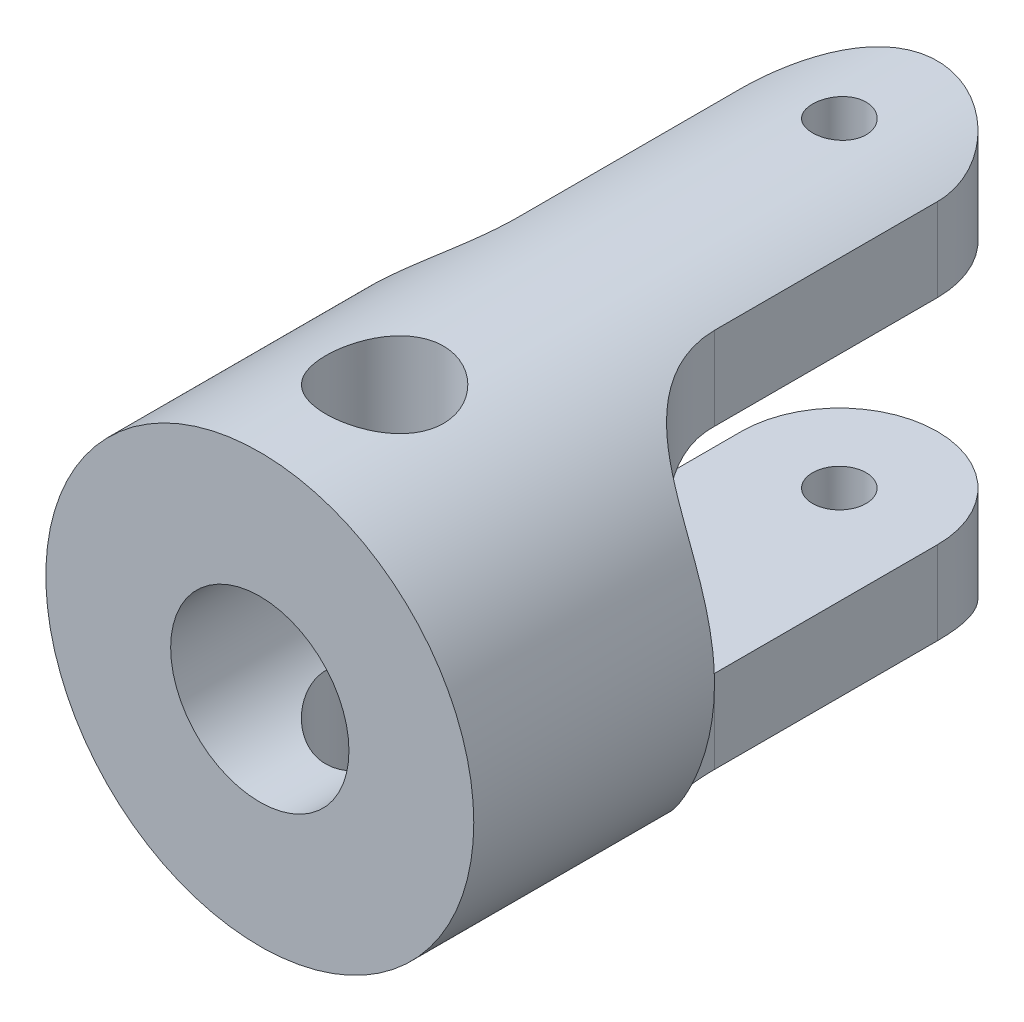
SolidWorks part; units mm, degrees
ref_plane "前视基准面" through (0, 0, 0) normal (0, 0, 1) x (1, 0, 0)
ref_plane "上视基准面" through (0, 0, 0) normal (0, 1, 0) x (1, 0, 0)
ref_plane "右视基准面" through (0, 0, 0) normal (1, 0, 0) x (0, 0, -1)
sketch "草图1" plane through (0, 0, 0) normal (0, 0, 1) x (1, 0, 0)
  circle A0 centre (0, 0) radius 6
  circle A1 centre (0, 0) radius 2.5
  dimension "D1" = 12
  dimension "D2" = 5
extrude "凸台-拉伸1" add sketch "草图1" along normal blind 19
sketch "草图2" plane through (0, 0, 0) normal (0, 1, 0) x (1, 0, 0)
  line L0 (0, 3.1848) -> (0, -21.7389) construction
  line L1 (-11.4446, -9) -> (14.3905, -9) construction
  line L2 (-2.75, -2.75) -> (-2.75, -9)
  line L4 (-6, 0) -> (-6, -19) construction
  line L5 (-6, -19) -> (6, -19) construction
  line L6 (-6, -2.0062) -> (-6, -15.979) construction
  line L7 (-6, -12.25) -> (-6, -19)
  line L8 (-6, -19) -> (6, -19)
  line L9 (6, -12.25) -> (6, -19)
  line L10 (2.75, -2.75) -> (2.75, -9)
  arc A0 (2.75, -2.75) -> (-2.75, -2.75) centre (0, -2.75) ccw
  arc A2 (-6, -12.25) -> (-2.75, -9) centre (-6, -9) ccw
  arc A3 (6, -12.25) -> (2.75, -9) centre (6, -9) cw
  circle A4 centre (0, -2.75) radius 0.75
  dimension "D1" = 5.5
  dimension "D2" = 10
  dimension "D3" = 1.5
extrude "切除-拉伸1" cut sketch "草图2" against normal mid plane 19 flip side to cut
sketch "草图3" plane through (0, 0, 0) normal (1, 0, 0) x (0, 0, -1)
  line L0 (-21.1395, 0) -> (4.4517, 0) construction
  line L1 (-9.25, 3) -> (0, 3)
  line L2 (0, 2.5) -> (0, 6) construction
  line L3 (0, 3) -> (0, -3)
  line L4 (0, -6) -> (0, -2.5) construction
  line L5 (0, -3) -> (-9.25, -3)
  arc A0 (-9.25, 3) -> (-9.25, -3) centre (-9.25, 0) ccw
  spline S1 degree 3 poles (-9, 5.3327) (-9.3489, 5.3327) (-9.6897, 5.3051) (-10.1779, 5.2159) (-10.3329, 5.1787) (-10.6283, 5.0872) (-10.7698, 5.0323) (-11.0313, 4.9047) (-11.1508, 4.8325) (-11.3691, 4.6696) (-11.4686, 4.5779) (-11.6436, 4.3792) (-11.7196, 4.2721) (-11.8523, 4.0422) (-11.9093, 3.9185) (-12.0526, 3.5326) (-12.1137, 3.2543) (-12.1762, 2.8069) (-12.192, 2.6524) (-12.2163, 2.34) (-12.2248, 2.1814) (-12.2435, 1.6983) (-12.2472, 1.3667) (-12.2504, 0.6843) (-12.25, 0.3412) (-12.25, -0.3433) (-12.2504, -0.687) (-12.2472, -1.3688) (-12.2435, -1.6999) (-12.2185, -2.3429) (-12.1972, -2.6566) (-12.1136, -3.2548) (-12.0524, -3.5333) (-11.9091, -3.9189) (-11.8521, -4.0427) (-11.7194, -4.2724) (-11.6436, -4.3792) (-11.4694, -4.577) (-11.3699, -4.6689) (-11.1511, -4.8323) (-11.032, -4.9042) (-10.7735, -5.0307) (-10.6328, -5.0857) (-10.3348, -5.1783) (-10.1798, -5.2154) (-9.8578, -5.2745) (-9.6895, -5.2965) (-9.3474, -5.3255) (-9.1746, -5.3327) (-9, -5.3327) knots 0 0 0 0 0.0625 0.0625 0.09375 0.09375 0.125 0.125 0.15625 0.15625 0.1875 0.1875 0.21875 0.21875 0.25 0.25 0.3125 0.3125 0.34375 0.34375 0.375 0.375 0.4375 0.4375 0.5 0.5 0.5625 0.5625 0.625 0.625 0.6875 0.6875 0.75 0.75 0.78125 0.78125 0.8125 0.8125 0.84375 0.84375 0.875 0.875 0.90625 0.90625 0.9375 0.9375 0.96875 0.96875 1 1 1 1 construction
  dimension "D1" = 6
extrude "切除-拉伸2" cut sketch "草图3" against normal mid plane 19
ref_plane "基准面1" through (0, 6, 0) normal (0, 1, 0) x (1, 0, 0)
sketch "草图5" plane through (0, 6, 0) normal (0, 1, 0) x (1, 0, 0)
  line L0 (0, 1.9633) -> (0, -21.1309) construction
  line L1 (-6, -19) -> (6, -19) construction
  circle A0 centre (0, -15.5) radius 2
  dimension "D1" = 3.5
  dimension "D2" = 4
hole_wizard "M4 螺纹孔1" positions "草图6" profile "草图7" tap size "M4" standard "GB"
sketch "草图6" plane through (0, 6, 0) normal (0, 1, 0) x (1, 0, 0)
  point P0 (0, -15.5)
sketch "草图7" plane through (0, 6, 15.5) normal (1, 0, 0) x (0, 0, 1)
  line L0 (0, 0) -> (0, 20.9914)
  line L1 (0, 20.9914) -> (1.65, 20)
  line L2 (1.65, 20) -> (1.65, 0)
  line L5 (1.65, 0) -> (0, 0)
  line L10 (0, 20.9914) -> (-1.65, 20) construction
  line L11 (0, -6.35) -> (0, 107.95) construction
  dimension "螺纹孔钻头直径" = 3.3
  dimension "螺纹孔钻头深度" = 20
  dimension "导头角度" = 118
cosmetic thread "孔螺蚊线1" parameters "D1"=8, "D2"=4
